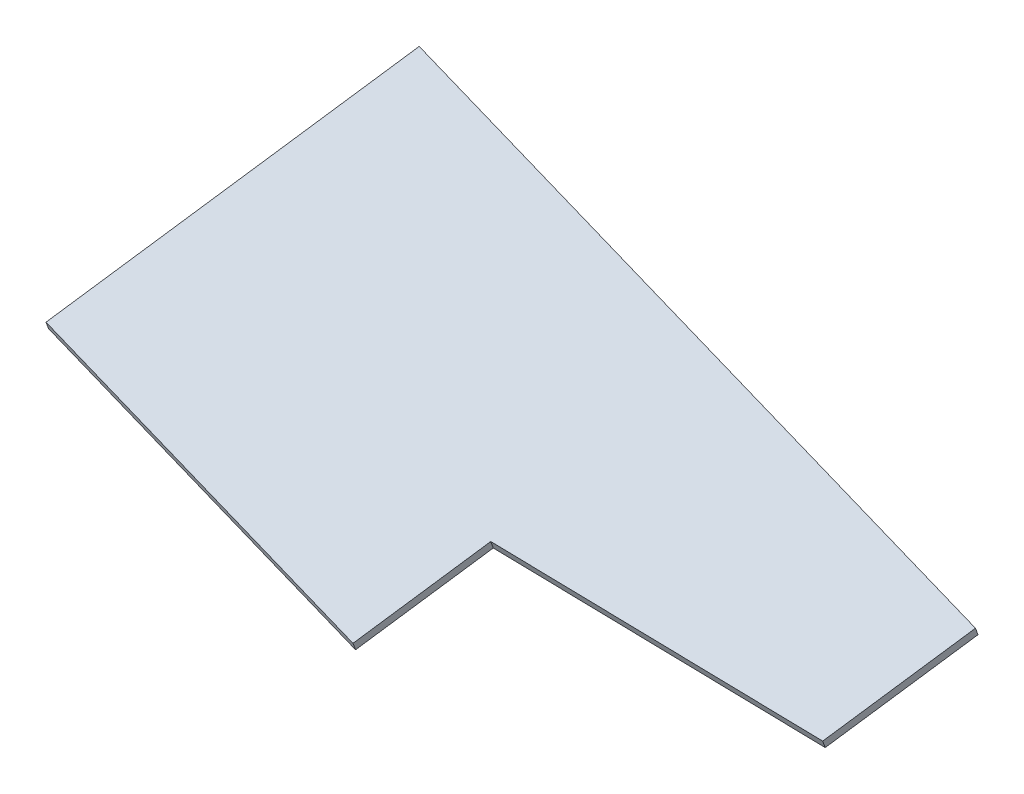
SolidWorks part; units mm, degrees
other "Markup1"
sketch "Sketch8" plane through (257.7307, 430.8513, 260.066) normal (0.119, 0.9518, 0.2826) x (0.9929, -0.114, -0.0339)
ref_plane "Front Plane" through (0, 0, 0) normal (0, 0, 1) x (1, 0, 0)
ref_plane "Top Plane" through (0, 0, 0) normal (0, 1, 0) x (1, 0, 0)
ref_plane "Right Plane" through (0, 0, 0) normal (1, 0, 0) x (0, 0, -1)
sketch "Sketch1" plane through (270.562, 2929.8684, 1339.313) normal (-0.0936, -0.9136, -0.3958) x (0.9339, -0.2183, 0.2831)
  line L8 (-317.0862, -434.4424) -> (-183.3657, -452.9851)
  line L9 (-317.0862, -434.4424) -> (-333.4628, -552.5423)
  line L10 (-183.3657, -452.9851) -> (-189.4101, -496.5746)
  line L11 (-333.4628, -552.5423) -> (-199.7423, -571.0849)
  line L12 (-184.8963, -464.0232) -> (-189.9184, -500.2401) construction
  line L13 (-312.1336, -435.1291) -> (-317.0862, -434.4424) construction
  line L14 (-328.5102, -553.229) -> (-333.4628, -552.5423) construction
  line L15 (-317.0862, -434.4424) -> (-333.4628, -552.5423) construction
  line L17 (-91.1811, -586.1389) -> (-199.7423, -571.0849)
  line L18 (-91.1811, -586.1389) -> (-84.477, -537.7925)
  line L19 (-69.2486, -427.9732) -> (-94.0367, -606.7321) construction
  line L20 (-189.4101, -496.5746) -> (-84.477, -537.7925)
  point P12 (-18.3316, -60.7849)
  point P13 (-16.2437, -45.728)
  point P16 (-121.1768, -4.5101)
  dimension "D1" = 244.6
  dimension "D2" = 75.2233
extrude "Boss-Extrude1" add sketch "Sketch1" against normal blind 3
